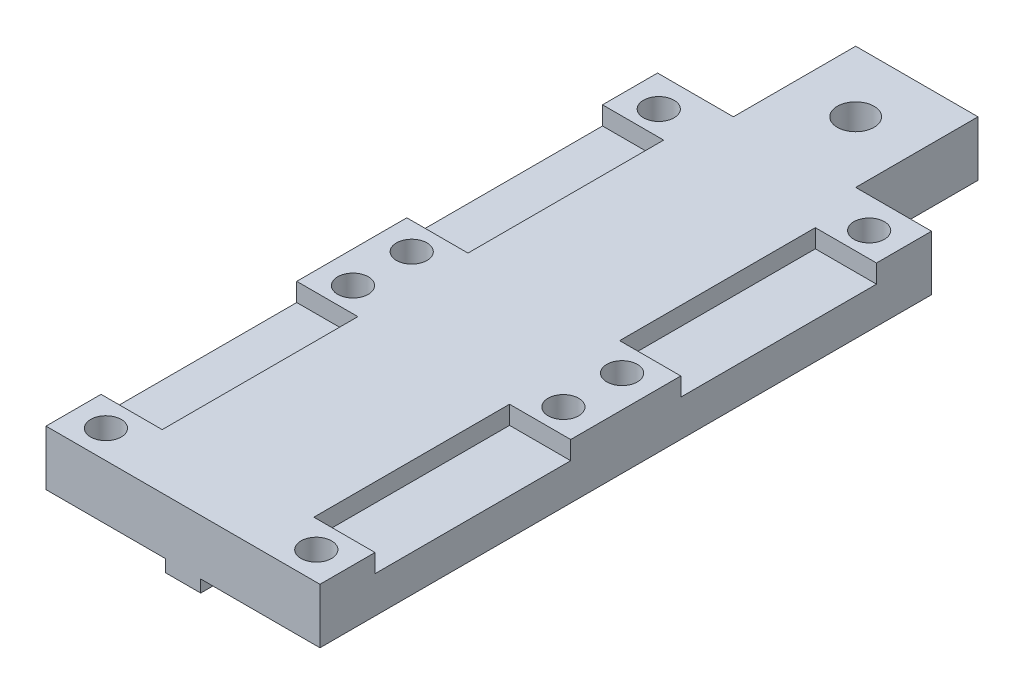
SolidWorks part; units mm, degrees
ref_plane "Front Plane" through (0, 0, 0) normal (0, 0, 1) x (1, 0, 0)
ref_plane "Top Plane" through (0, 0, 0) normal (0, 1, 0) x (1, 0, 0)
ref_plane "Right Plane" through (0, 0, 0) normal (1, 0, 0) x (0, 0, -1)
sketch "Sketch1" plane through (0, 0, 0) normal (0, 0, 1) x (1, 0, 0)
  line L0 (-11.2, 1) -> (-1.45, 1)
  line L1 (-1.45, 1) -> (-1.45, 0)
  line L2 (-1.45, 0) -> (1.45, 0)
  line L3 (1.45, 0) -> (1.45, 1)
  line L4 (1.45, 1) -> (11.2, 1)
  line L5 (11.2, 1) -> (11.2, 5.5)
  line L6 (11.2, 5.5) -> (-11.2, 5.5)
  line L7 (-11.2, 5.5) -> (-11.2, 1)
  point P8 (0, 0)
  point P9 (0, 0)
  point P11 (0, 0)
  dimension "D1" = 2.9
  dimension "D2" = 1
  dimension "D3" = 22.4
  dimension "D4" = 4.5
extrude "Boss-Extrude1" add sketch "Sketch1" along normal mid plane 60
sketch "Sketch3" plane through (0, 5.5, 0) normal (0, 1, 0) x (1, 0, 0)
  line L0 (11.2, 30) -> (-11.2, 30) construction
  line L2 (-11.2, 30) -> (-5, 30)
  line L3 (-11.2, 30) -> (-11.2, 20)
  line L4 (-11.2, 20) -> (-5, 20)
  line L5 (-5, 30) -> (-5, 20)
  line L6 (11.2, 30) -> (5, 30)
  line L7 (11.2, 30) -> (11.2, 20)
  line L8 (11.2, 20) -> (5, 20)
  line L9 (5, 30) -> (5, 20)
  circle A0 centre (0, 25) radius 1.5
  dimension "D1" = 3
  dimension "D2" = 5
  dimension "D3" = 10
  dimension "D4" = 10
extrude "MakerBeamFix" cut sketch "Sketch3" against normal through all
sketch "Sketch4" plane through (0, 5.5, 0) normal (0, 1, 0) x (1, 0, 0)
  line L0 (-8.6, 17.5) -> (8.6, 17.5) construction
  line L1 (-11.2, 20) -> (-5, 20) construction
  circle A0 centre (-8.6, 17.5) radius 1.25
  circle A1 centre (8.6, 17.5) radius 1.25
  circle A2 centre (-8.6, -2.7) radius 1.25
  circle A3 centre (8.6, -2.7) radius 1.25
  point P8 (0, 17.5)
  point P9 (0, 0)
  dimension "D1" = 17.2
  dimension "D4" = 2.5
  dimension "D2" = 20.2
  dimension "D3" = 2.5
extrude "FixHoles" cut sketch "Sketch4" against normal through all
sketch "Sketch5" plane through (0, 5.5, 0) normal (0, 1, 0) x (1, 0, 0)
  line L0 (-11.2, -30) -> (-11.2, 20) construction
  line L1 (-11.2, 15.5) -> (-6.2, 15.5)
  line L2 (-11.2, 15.5) -> (-11.2, -0.5)
  line L3 (-11.2, -0.5) -> (-6.2, -0.5)
  line L4 (-6.2, 15.5) -> (-6.2, -0.5)
  line L5 (11.2, -30) -> (11.2, 20) construction
  line L6 (6.2, 15.5) -> (11.2, 15.5)
  line L7 (6.2, 15.5) -> (6.2, -0.5)
  line L8 (6.2, -0.5) -> (11.2, -0.5)
  line L9 (11.2, 15.5) -> (11.2, -0.5)
  line L10 (-11.2, 20) -> (-5, 20) construction
  dimension "D1" = 16
  dimension "D2" = 4.5
  dimension "D3" = 5
  dimension "D4" = 5
extrude "PinFixHoles" cut sketch "Sketch5" against normal blind 1.5
pattern_linear "LPattern1" count 2 spacing 25 along (0, 0, 1) of "FixHoles", "PinFixHoles"
